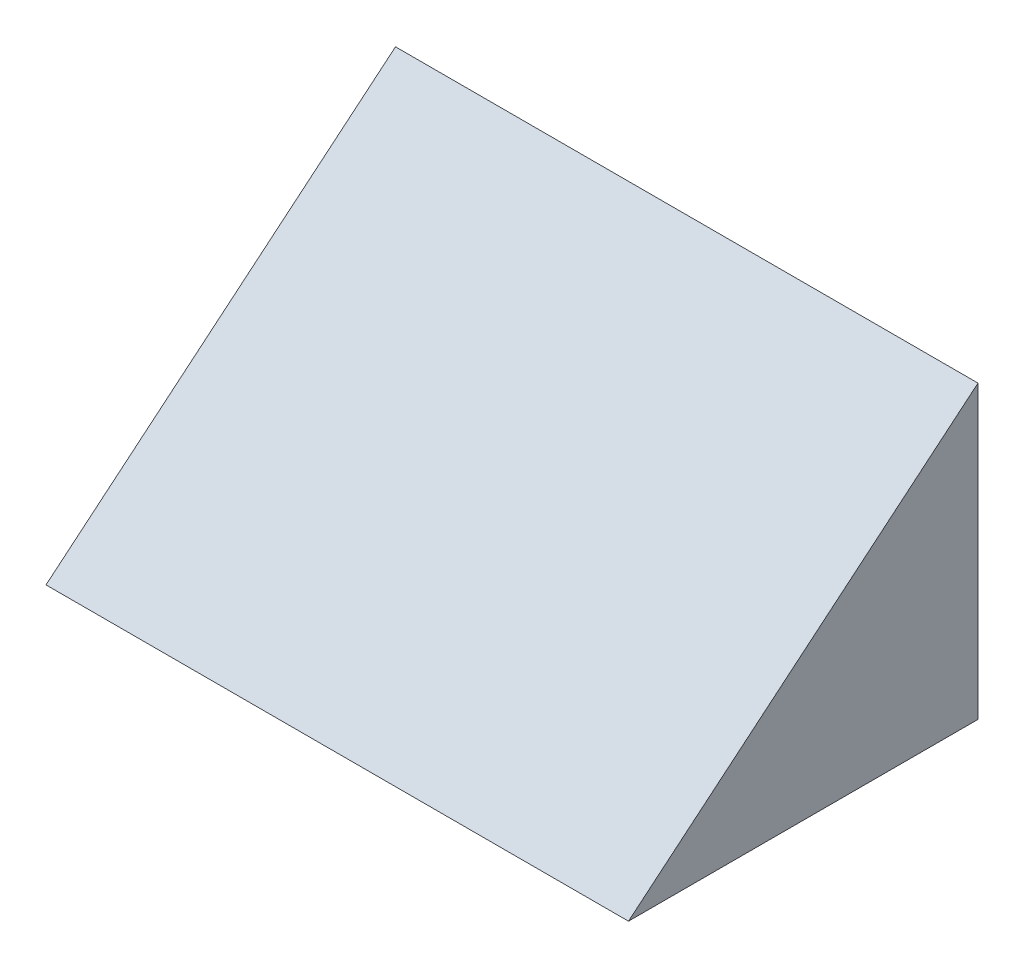
SolidWorks part; units mm, degrees
ref_plane "Front Plane" through (0, 0, 0) normal (0, 0, 1) x (1, 0, 0)
ref_plane "Top Plane" through (0, 0, 0) normal (0, 1, 0) x (1, 0, 0)
ref_plane "Right Plane" through (0, 0, 0) normal (1, 0, 0) x (0, 0, -1)
sketch "Sketch1" plane through (0, 0, 0) normal (1, 0, 0) x (0, 0, -1)
  line L0 (0, 0) -> (0, 100)
  line L1 (0, 100) -> (-120, 0)
  line L2 (-120, 0) -> (0, 0)
  dimension "D1" = 100
  dimension "D2" = 120
extrude "Boss-Extrude1" add sketch "Sketch1" along normal blind 200
